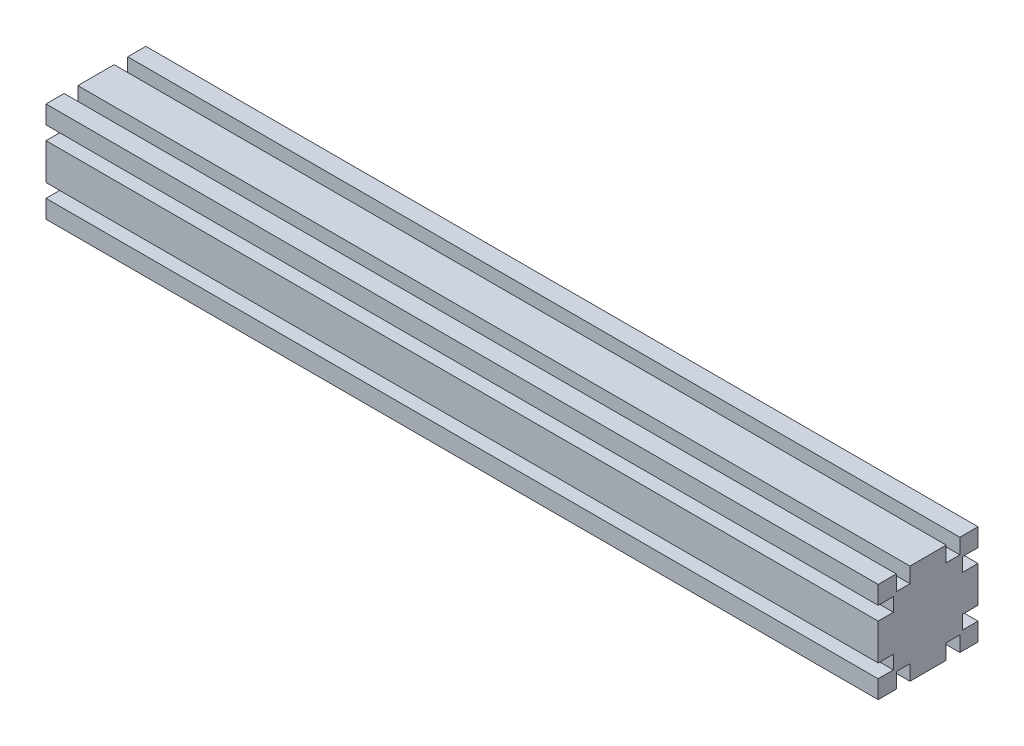
SolidWorks part; units mm, degrees
ref_plane "前视基准面" through (0, 0, 0) normal (0, 0, 1) x (1, 0, 0)
ref_plane "上视基准面" through (0, 0, 0) normal (0, 1, 0) x (1, 0, 0)
ref_plane "右视基准面" through (0, 0, 0) normal (1, 0, 0) x (0, 0, -1)
sketch "草图1" plane through (0, 0, 0) normal (1, 0, 0) x (0, 0, -1)
  line L1 (-30, 30) -> (30, 30)
  line L2 (-30, 30) -> (-30, -30)
  line L3 (-30, -30) -> (30, -30)
  line L4 (30, 30) -> (30, -30)
  line L5 (-30, 30) -> (30, -30) construction
  line L6 (-30, -30) -> (30, 30) construction
  point P0 (0, 0)
  dimension "D1" = 60
  dimension "60" = 60
extrude "凸台-拉伸1" add sketch "草图1" along normal blind 500
sketch "草图2" plane through (0, 0, 0) normal (-1, 0, 0) x (0, 0, 1)
  line L0 (-19.1, 30) -> (-19.1, 20.8)
  line L1 (-30, 30) -> (30, 30) construction
  line L2 (-19.1, 20.8) -> (-10.9, 20.8)
  line L3 (-10.9, 20.8) -> (-10.9, 30)
  line L4 (-19.1, 30) -> (-10.9, 30)
  line L5 (0, -47.1527) -> (0, 0) construction
  line L6 (0, 0) -> (0, 44.4053) construction
  line L7 (0, 0) -> (71.4438, 0) construction
  line L8 (0, 0) -> (-65.6472, 0) construction
  line L9 (-19.1, -20.8) -> (-10.9, -20.8)
  line L10 (-10.9, -20.8) -> (-10.9, -30)
  line L11 (-19.1, -30) -> (-19.1, -20.8)
  line L12 (-19.1, -30) -> (-10.9, -30)
  line L13 (19.1, -30) -> (10.9, -30)
  line L14 (10.9, -20.8) -> (10.9, -30)
  line L15 (19.1, -30) -> (19.1, -20.8)
  line L16 (19.1, -20.8) -> (10.9, -20.8)
  line L17 (19.1, 20.8) -> (10.9, 20.8)
  line L18 (19.1, 30) -> (19.1, 20.8)
  line L19 (19.1, 30) -> (10.9, 30)
  line L20 (10.9, 20.8) -> (10.9, 30)
  line L21 (-30, 19.1) -> (-20.8, 19.1)
  line L22 (-30, -30) -> (-30, 30) construction
  line L23 (-20.8, 19.1) -> (-20.8, 10.9)
  line L24 (-20.8, 10.9) -> (-30, 10.9)
  line L25 (-30, 10.9) -> (-30, 19.1)
  line L26 (-30, -10.9) -> (-30, -19.1)
  line L27 (-20.8, -10.9) -> (-30, -10.9)
  line L28 (-20.8, -19.1) -> (-20.8, -10.9)
  line L29 (-30, -19.1) -> (-20.8, -19.1)
  line L30 (30, -19.1) -> (20.8, -19.1)
  line L31 (20.8, -19.1) -> (20.8, -10.9)
  line L32 (20.8, -10.9) -> (30, -10.9)
  line L33 (30, -10.9) -> (30, -19.1)
  line L34 (30, 10.9) -> (30, 19.1)
  line L35 (20.8, 10.9) -> (30, 10.9)
  line L36 (20.8, 19.1) -> (20.8, 10.9)
  line L37 (30, 19.1) -> (20.8, 19.1)
  dimension "D1" = 10.9
  dimension "D2" = 8.2
  dimension "D3" = 9.2
  dimension "D4" = 8.2
  dimension "D5" = 9.2
  dimension "D6" = 10.9
extrude "切除-拉伸1" cut sketch "草图2" against normal through all
sketch "草图3" plane through (0, 0, 30) normal (0, 0, 1) x (1, 0, 0)
  line L0 (0, 30) -> (60, -30)
  line L1 (500, -30) -> (0, -30) construction
  line L2 (0, 30) -> (0, -30)
  line L3 (0, -30) -> (60, -30)
  line L4 (500, 30) -> (500, -30)
  line L5 (500, -30) -> (440, -30)
  line L6 (440, -30) -> (500, 30)
  dimension "D1" = 45
  dimension "D2" = 45
sketch "草图4" plane through (0, 30, 0) normal (0, 1, 0) x (1, 0, 0)
  line L0 (0, 15) -> (500, 15)
  line L1 (0, 19.1) -> (0, 10.9) construction
  line L2 (500, 19.1) -> (500, 10.9) construction
  line L3 (500, 15) -> (500, -15)
  line L4 (500, -10.9) -> (500, -19.1) construction
  line L5 (500, -15) -> (0, -15)
  line L6 (0, -10.9) -> (0, -19.1) construction
sketch "草图5" plane through (0, 30, 0) normal (0, 1, 0) x (1, 0, 0)
  line L0 (0, 0) -> (500, 0)
  line L1 (500, 15) -> (500, -15) construction
  line L2 (250, 0) -> (250, 205.1554)
